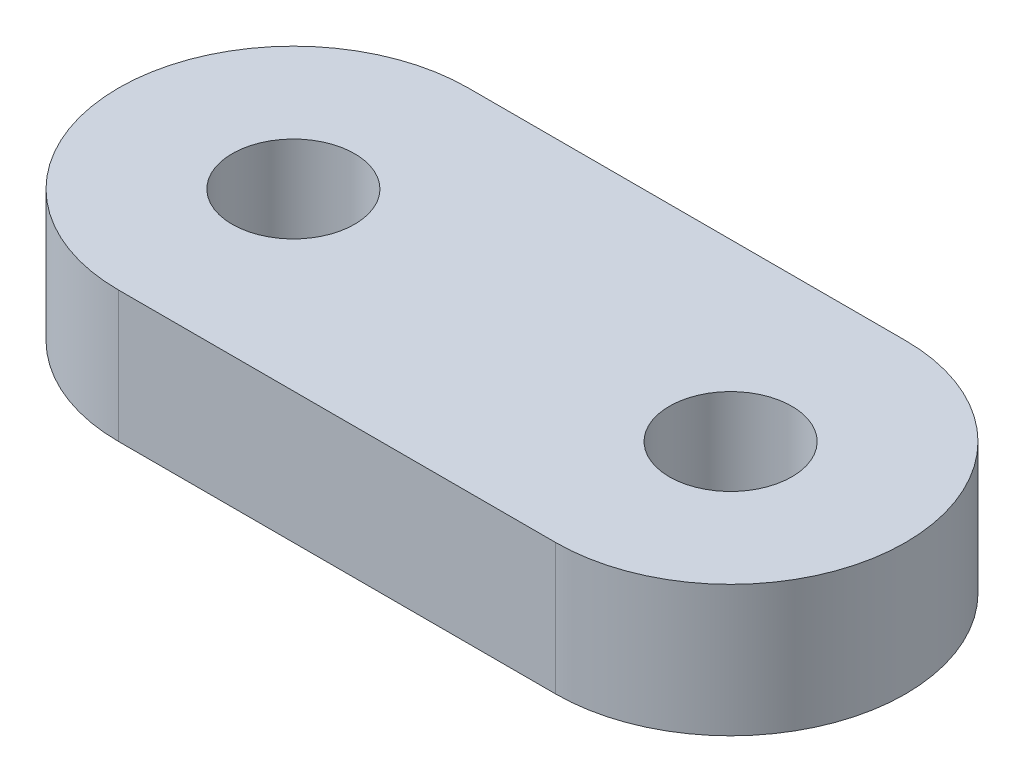
SolidWorks part; units mm, degrees
ref_plane "Front Plane" through (0, 0, 0) normal (0, 0, 1) x (1, 0, 0)
ref_plane "Top Plane" through (0, 0, 0) normal (0, 1, 0) x (1, 0, 0)
ref_plane "Right Plane" through (0, 0, 0) normal (1, 0, 0) x (0, 0, -1)
sketch "Sketch1" plane through (0, 0, 0) normal (0, 1, 0) x (1, 0, 0)
  line L0 (5.0009, 3.9989) -> (-4.9991, 4.0011)
  line L1 (-5.0009, -3.9989) -> (4.9991, -4.0011)
  arc A0 (-4.9991, 4.0011) -> (-5.0009, -3.9989) centre (-5, 0.0011) ccw
  arc A1 (4.9991, -4.0011) -> (5.0009, 3.9989) centre (5, -0.0011) ccw
  circle A2 centre (5, -0.0011) radius 1.4
  circle A3 centre (-5, 0.0011) radius 1.4
  dimension "D1" = 2.8
  dimension "D3" = 2.8
  dimension "D2" = 10
extrude "Boss-Extrude1" add sketch "Sketch1" along normal blind 3
